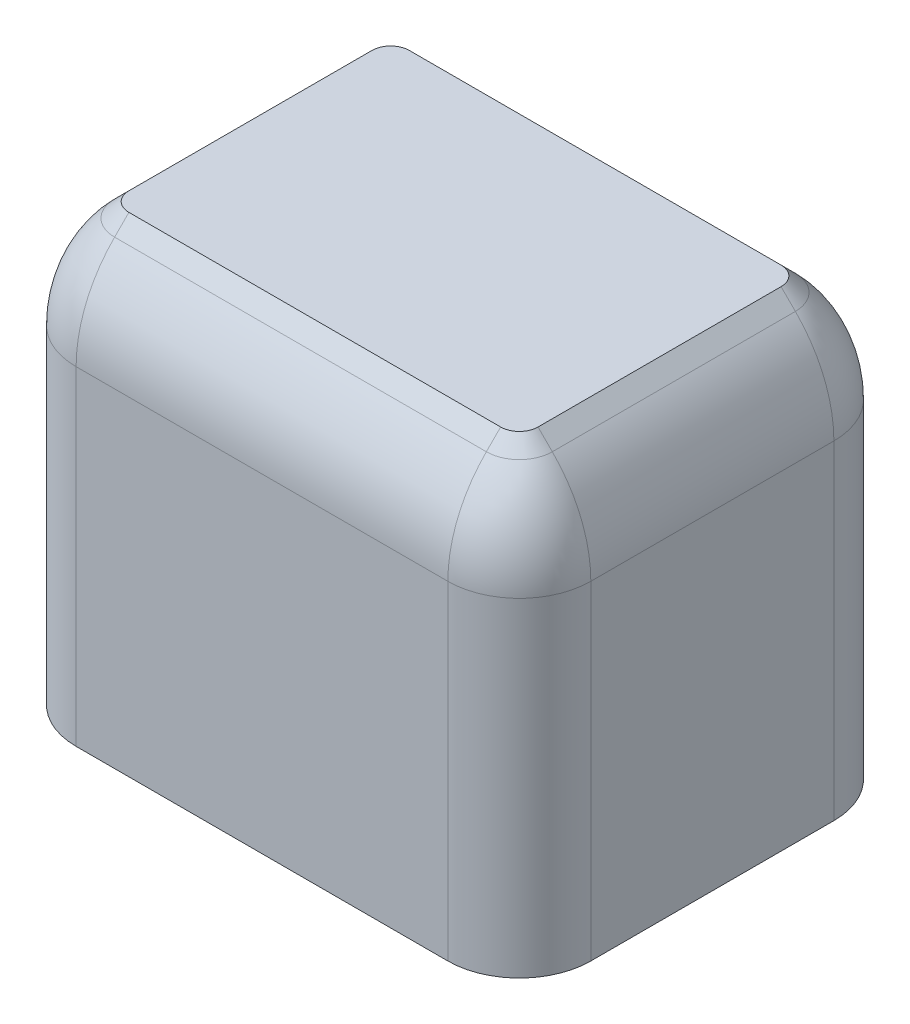
SolidWorks part; units mm, degrees
ref_plane "Front Plane" through (0, 0, 0) normal (0, 0, 1) x (1, 0, 0)
ref_plane "Top Plane" through (0, 0, 0) normal (0, 1, 0) x (1, 0, 0)
ref_plane "Right Plane" through (0, 0, 0) normal (1, 0, 0) x (0, 0, -1)
sketch "Sketch1" plane through (0, 0, 0) normal (0, 1, 0) x (1, 0, 0)
  line L0 (0, -2.1) -> (0, 2.1) construction
  line L1 (-2.15, 0) -> (2.15, 0) construction
  line L2 (-0.675, 0.975) -> (-0.675, 2.1)
  line L3 (-0.675, -2.1) -> (0.675, -2.1)
  line L4 (-0.675, -2.1) -> (-0.675, -0.975)
  line L5 (-0.675, 2.1) -> (0.675, 2.1)
  line L6 (0.675, -2.1) -> (0.675, -0.975)
  line L7 (-0.675, -2.1) -> (0.675, 2.1) construction
  line L8 (-0.675, 2.1) -> (0.675, -2.1) construction
  line L9 (-2.15, -0.675) -> (-0.975, -0.675)
  line L10 (-2.15, -0.675) -> (-2.15, 0.675)
  line L11 (-2.15, 0.675) -> (-0.975, 0.675)
  line L12 (2.15, -0.675) -> (2.15, 0.675)
  line L13 (-2.15, -0.675) -> (2.15, 0.675) construction
  line L14 (-2.15, 0.675) -> (2.15, -0.675) construction
  line L15 (0.975, 0.675) -> (2.15, 0.675)
  line L16 (0.675, 0.975) -> (0.675, 2.1)
  line L17 (0.975, -0.675) -> (2.15, -0.675)
  line L24 (-3.6, -2.7) -> (3.6, -2.7)
  line L30 (-3.6, -2.7) -> (-3.6, 2.7)
  line L32 (-3.6, 2.7) -> (3.6, 2.7)
  line L33 (3.6, -2.7) -> (3.6, 2.7)
  line L34 (-3.6, -2.7) -> (3.6, 2.7) construction
  line L35 (-3.6, 2.7) -> (3.6, -2.7) construction
  arc A1 (-0.675, -0.975) -> (-0.975, -0.675) centre (-0.975, -0.975) ccw
  arc A2 (0.675, -0.975) -> (0.975, -0.675) centre (0.975, -0.975) cw
  arc A3 (0.975, 0.675) -> (0.675, 0.975) centre (0.975, 0.975) cw
  arc A4 (-0.675, 0.975) -> (-0.975, 0.675) centre (-0.975, 0.975) cw
  point P0 (0, 0)
  point P1 (0, 0)
  point P5 (0, 0)
  point P8 (0, 0)
  point P20 (2.15, 0)
  point P21 (0, 2.1)
  dimension "D1" = 4.3
  dimension "D4" = 0.3
  dimension "D6" = 4.2
  dimension "D2" = 5.4
  dimension "D3" = 1.35
  dimension "D5" = 7.2
extrude "stem housing" add sketch "Sketch1" along normal blind 4.5
sketch "Sketch3" plane through (0, 4.5, 0) normal (0, 1, 0) x (1, 0, 0)
  line L8 (3.6, 2.7) -> (-3.6, 2.7)
  line L9 (3.6, 2.7) -> (-3.6, 2.7)
  line L16 (-3.6, -2.7) -> (3.6, -2.7)
  line L18 (3.6, -2.7) -> (3.6, 2.7)
  line L21 (-3.6, 2.7) -> (-3.6, -2.7)
  line L22 (-3.6, -2.7) -> (3.6, -2.7)
  line L24 (3.6, -2.7) -> (3.6, 2.7)
  line L27 (-3.6, 2.7) -> (-3.6, -2.7)
  dimension "D1" = 0
extrude "Boss-Extrude2" add sketch "Sketch3" along normal blind 1.6
sketch "Sketch4" plane through (0, 0, 0) normal (0, 0, 1) x (1, 0, 0)
  line L0 (-2.8615, 6.1) -> (-3.0615, 5.9)
  line L1 (-3.6, 6.1) -> (3.6, 6.1) construction
  line L2 (-3.6, 6.1) -> (-3.6, 0) construction
  line L3 (-2.8615, 6.1) -> (-3.6, 6.1)
  line L4 (-3.6, 6.1) -> (-3.6, 4.6)
  arc A0 (-3.0615, 5.9) -> (-3.6, 4.6) centre (-1.7615, 4.6) ccw
  dimension "D1" = 45
  dimension "D2" = 0.2
  dimension "D3" = 1.5
fillet "Fillet2" radius 1 4 edges at (-3.6, 3.05, -2.7) (3.6, 3.05, -2.7) (3.6, 3.05, 2.7) (-3.6, 3.05, 2.7)
sketch "Sketch6" plane through (0, 6.1, 0) normal (0, 1, 0) x (1, 0, 0)
  line L21 (-2.6, -2.7) -> (2.6, -2.7)
  line L22 (-3.6, 1.7) -> (-3.6, -1.7)
  line L23 (3.6, -1.7) -> (3.6, 1.7)
  line L24 (2.6, 2.7) -> (-2.6, 2.7)
  line L25 (-2.6, -2.7) -> (2.6, -2.7)
  line L26 (-3.6, 1.7) -> (-3.6, -1.7)
  line L27 (3.6, -1.7) -> (3.6, 1.7)
  line L28 (2.6, 2.7) -> (-2.6, 2.7)
  arc A23 (2.6, -2.7) -> (3.6, -1.7) centre (2.6, -1.7) ccw
  arc A24 (-3.6, -1.7) -> (-2.6, -2.7) centre (-2.6, -1.7) ccw
  arc A25 (3.6, 1.7) -> (2.6, 2.7) centre (2.6, 1.7) ccw
  arc A26 (-2.6, 2.7) -> (-3.6, 1.7) centre (-2.6, 1.7) ccw
  arc A27 (2.6, -2.7) -> (3.6, -1.7) centre (2.6, -1.7) ccw
  arc A28 (-3.6, -1.7) -> (-2.6, -2.7) centre (-2.6, -1.7) ccw
  arc A29 (3.6, 1.7) -> (2.6, 2.7) centre (2.6, 1.7) ccw
  arc A30 (-2.6, 2.7) -> (-3.6, 1.7) centre (-2.6, 1.7) ccw
  dimension "D1" = 0
sweep "Cut-Sweep1" cut profiles "Sketch4" path "Sketch6"
